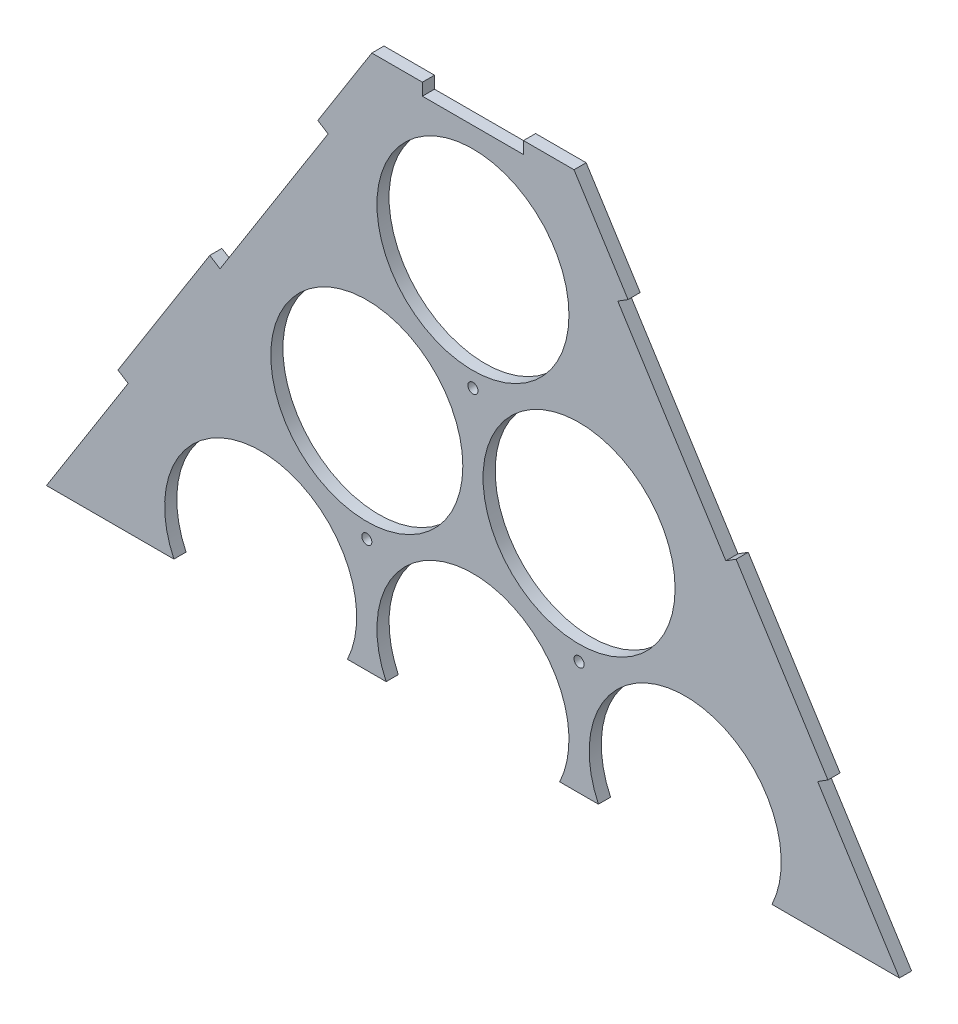
SolidWorks part; units mm, degrees
ref_plane "Plan de face" through (0, 0, 0) normal (0, 0, 1) x (1, 0, 0)
ref_plane "Plan de dessus" through (0, 0, 0) normal (0, 1, 0) x (1, 0, 0)
ref_plane "Plan de droite" through (0, 0, 0) normal (1, 0, 0) x (0, 0, -1)
sketch "Esquisse1" plane through (0, 0, 0) normal (0, 0, 1) x (1, 0, 0)
  line L0 (0, 0) -> (-371.1464, 0) construction
  line L1 (0, 0) -> (478.5179, 0) construction
  line L2 (0, 0) -> (0, 90.9327) construction
  line L3 (0, 90.9327) -> (-157.5, 90.9327) construction
  line L4 (0, 90.9327) -> (157.5, 90.9327) construction
  line L5 (0, 90.9327) -> (0, 181.8653) construction
  line L6 (0, 181.8653) -> (-52.5, 181.8653) construction
  line L7 (0, 181.8653) -> (52.5, 181.8653) construction
  line L8 (0, 181.8653) -> (0, 363.4062) construction
  line L12 (-255.7759, 10.9597) -> (-205, -75.1903)
  line L13 (205, -75.1903) -> (255.7759, 10.9597)
  line L14 (-50, 336.3537) -> (50, 336.3537)
  line L15 (-205, -75.1903) -> (205, -75.1903)
  line L16 (255.7759, 10.9597) -> (50, 336.3537)
  line L17 (-50, 336.3537) -> (-255.7759, 10.9597)
  line L18 (-50, 336.3537) -> (-50, -75.1903) construction
  line L19 (50, 336.3537) -> (50, -75.1903) construction
  circle A0 centre (-157.5, 0) radius 47.5
  circle A1 centre (-52.5, 0) radius 47.5
  circle A2 centre (52.5, 0) radius 47.5
  circle A3 centre (157.5, 0) radius 47.5
  circle A4 centre (-105, 90.9327) radius 47.5
  circle A5 centre (0, 90.9327) radius 47.5
  circle A6 centre (105, 90.9327) radius 47.5
  circle A7 centre (-52.5, 181.8653) radius 47.5
  circle A8 centre (52.5, 181.8653) radius 47.5
  circle A9 centre (0, 272.798) radius 47.5
  dimension "D1" = 95
  dimension "D2" = 95
  dimension "D3" = 95
  dimension "D4" = 95
  dimension "D5" = 105
  dimension "D6" = 52.5
  dimension "D7" = 52.5
  dimension "D8" = 105
  dimension "D9" = 95
  dimension "D10" = 95
  dimension "D11" = 95
  dimension "D12" = 105
  dimension "D13" = 105
  dimension "D14" = 105
  dimension "D15" = 95
  dimension "D16" = 95
  dimension "D17" = 105
  dimension "D18" = 52.5
  dimension "D19" = 52.5
  dimension "D20" = 95
  dimension "D21" = 105
  dimension "D27" = 205
  dimension "D22" = 385
  dimension "D23" = 385
  dimension "D24" = 410
  dimension "D25" = 32.309
  dimension "D26" = 32.309
  dimension "D28" = 100
  dimension "D30" = 100
  dimension "D31" = 100
extrude "Boss.-Extru.1" add sketch "Esquisse1" along normal blind 6
sketch "Esquisse9" plane through (0, 0, 6) normal (0, 0, 1) x (1, 0, 0)
  line L0 (-205, -75.1903) -> (205, -75.1903) construction
  line L1 (-75, -75.1903) -> (75, -75.1903)
  line L2 (-75, -75.1903) -> (-75, -195.1903)
  line L3 (-75, -195.1903) -> (75, -195.1903)
  line L4 (75, -75.1903) -> (75, -195.1903)
  dimension "D1" = 150
  dimension "D2" = 120
  dimension "D3" = 75
extrude "Boss.-Extru.2" add sketch "Esquisse9" against normal blind 10
sketch "Esquisse10" plane through (0, 0, 6) normal (0, 0, 1) x (1, 0, 0)
  line L0 (-75, -75.1903) -> (-75, -195.1903) construction
  line L1 (-75, -104.2447) -> (-69, -104.2447)
  line L2 (-75, -104.2447) -> (-75, -154.2447)
  line L3 (-75, -154.2447) -> (-69, -154.2447)
  line L4 (-69, -104.2447) -> (-69, -154.2447)
  line L5 (-75, -195.1903) -> (75, -195.1903) construction
  line L6 (-25, -195.1903) -> (25, -195.1903)
  line L7 (-25, -195.1903) -> (-25, -189.1903)
  line L8 (-25, -189.1903) -> (25, -189.1903)
  line L9 (25, -195.1903) -> (25, -189.1903)
  line L10 (-205, -75.1903) -> (-75, -75.1903) construction
  line L11 (-115, -75.1903) -> (-165, -75.1903)
  line L12 (-115, -75.1903) -> (-115, -69.1903)
  line L13 (-115, -69.1903) -> (-165, -69.1903)
  line L14 (-165, -75.1903) -> (-165, -69.1903)
  line L15 (-217.694, -53.6528) -> (-212.525, -50.6062)
  line L16 (-255.7759, 10.9597) -> (-205, -75.1903) construction
  line L17 (-212.525, -50.6062) -> (-237.9129, -7.5313)
  line L18 (-237.9129, -7.5313) -> (-243.0819, -10.5778)
  line L19 (-243.0819, -10.5778) -> (-217.694, -53.6528)
  line L20 (-229.0517, 53.2187) -> (-223.9806, 50.0118)
  line L21 (-50, 336.3537) -> (-255.7759, 10.9597) construction
  line L22 (-223.9806, 50.0118) -> (-170.5324, 134.5297)
  line L23 (-170.5324, 134.5297) -> (-175.6034, 137.7366)
  line L24 (-175.6034, 137.7366) -> (-229.0517, 53.2187)
  line L25 (-130.1724, 209.5768) -> (-125.1013, 206.3699)
  line L26 (-125.1013, 206.3699) -> (-71.6531, 290.8879)
  line L27 (-71.6531, 290.8879) -> (-76.7241, 294.0948)
  line L28 (-76.7241, 294.0948) -> (-130.1724, 209.5768)
  line L29 (50, 336.3537) -> (-50, 336.3537) construction
  line L30 (-25, 336.3537) -> (25, 336.3537)
  line L31 (-25, 336.3537) -> (-25, 330.3537)
  line L32 (-25, 330.3537) -> (25, 330.3537)
  line L33 (25, 336.3537) -> (25, 330.3537)
  line L34 (0, 336.3537) -> (0, -195.1903) construction
  line L35 (71.6531, 290.8879) -> (76.7241, 294.0948)
  line L36 (125.1013, 206.3699) -> (71.6531, 290.8879)
  line L37 (130.1724, 209.5768) -> (125.1013, 206.3699)
  line L38 (76.7241, 294.0948) -> (130.1724, 209.5768)
  line L39 (170.5324, 134.5297) -> (175.6034, 137.7366)
  line L40 (223.9806, 50.0118) -> (170.5324, 134.5297)
  line L41 (229.0517, 53.2187) -> (223.9806, 50.0118)
  line L42 (175.6034, 137.7366) -> (229.0517, 53.2187)
  line L43 (237.9129, -7.5313) -> (243.0819, -10.5778)
  line L44 (212.525, -50.6062) -> (237.9129, -7.5313)
  line L45 (217.694, -53.6528) -> (212.525, -50.6062)
  line L46 (243.0819, -10.5778) -> (217.694, -53.6528)
  line L47 (115, -69.1903) -> (165, -69.1903)
  line L48 (165, -75.1903) -> (165, -69.1903)
  line L49 (115, -75.1903) -> (165, -75.1903)
  line L50 (115, -75.1903) -> (115, -69.1903)
  line L51 (75, -154.2447) -> (69, -154.2447)
  line L52 (69, -104.2447) -> (69, -154.2447)
  line L53 (75, -104.2447) -> (69, -104.2447)
  line L54 (75, -104.2447) -> (75, -154.2447)
  dimension "D1" = 50
  dimension "D2" = 6
  dimension "D3" = 25
  dimension "D4" = 50
  dimension "D5" = 6
  dimension "D6" = 6
  dimension "D7" = 6
  dimension "D8" = 50
  dimension "D9" = 100
  dimension "D10" = 6
  dimension "D11" = 6
  dimension "D12" = 100
  dimension "D13" = 50
  dimension "D14" = 6
  dimension "D15" = 25
  dimension "D16" = 50
  dimension "D17" = 50
  dimension "D18" = 25
  dimension "D19" = 40
  dimension "D20" = 50
extrude "Enlèv. mat.-Extru.1" cut sketch "Esquisse10" against normal blind 10
sketch "Esquisse11" plane through (0, 0, 6) normal (0, 0, 1) x (1, 0, 0)
  line L1 (314.7687, -195.1903) -> (-355.4853, -195.1903)
  line L2 (314.7687, -195.1903) -> (314.7687, 70.5817)
  line L3 (314.7687, 70.5817) -> (-355.4853, 70.5817)
  line L4 (-355.4853, -195.1903) -> (-355.4853, 70.5817)
  dimension "D1" = 265.772
extrude "Enlèv. mat.-Extru.2" cut sketch "Esquisse11" against normal blind 10
sketch "Esquisse12" plane through (0, 0, 6) normal (0, 0, 1) x (1, 0, 0)
  circle A0 centre (-52.5, 126.8653) radius 2.5
  circle A1 centre (-52.5, 181.8653) radius 47.5 construction
  circle A2 centre (52.5, 126.8653) radius 2.5
  circle A3 centre (0, 217.798) radius 2.5
  circle A4 centre (0, 272.798) radius 47.5 construction
  dimension "D1" = 5
  dimension "D2" = 55
  dimension "D4" = 5
  dimension "D5" = 55
  dimension "D3" = 2
extrude "Enlèv. mat.-Extru.3" cut sketch "Esquisse12" against normal blind 10
